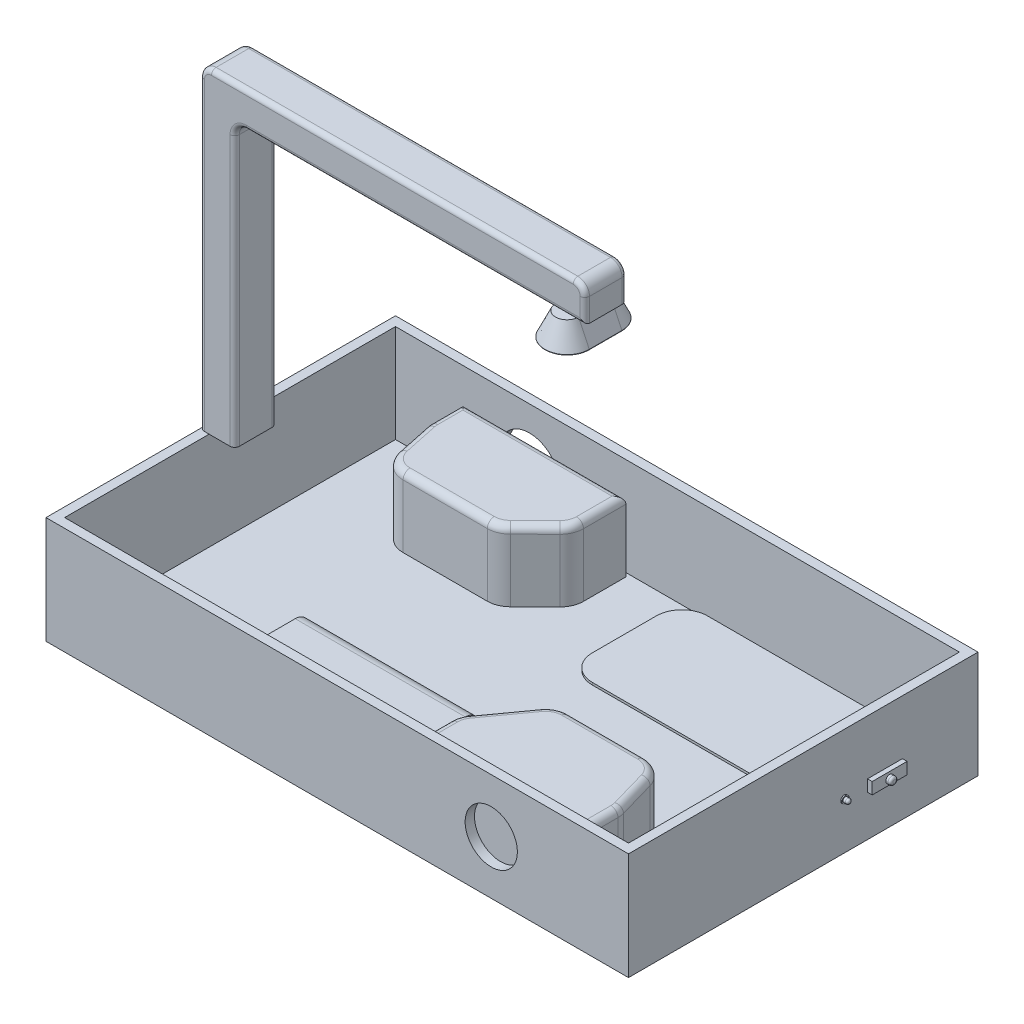
SolidWorks part; units mm, degrees
ref_plane "Front Plane" through (0, 0, 0) normal (0, 0, 1) x (1, 0, 0)
ref_plane "Top Plane" through (0, 0, 0) normal (0, 1, 0) x (1, 0, 0)
ref_plane "Right Plane" through (0, 0, 0) normal (1, 0, 0) x (0, 0, -1)
sketch "Sketch2" plane through (0, 0, 0) normal (0, 1, 0) x (1, 0, 0)
  line L1 (-125, 75) -> (125, 75)
  line L2 (-125, 75) -> (-125, -75)
  line L3 (-125, -75) -> (125, -75)
  line L4 (125, 75) -> (125, -75)
  line L5 (-125, 75) -> (125, -75) construction
  line L6 (-125, -75) -> (125, 75) construction
  point P0 (0, 0)
  dimension "D1" = 150
  dimension "D2" = 250
extrude "Boss-Extrude1" add sketch "Sketch2" along normal blind 4
sketch "Sketch3" plane through (0, 4, 0) normal (0, 1, 0) x (1, 0, 0)
  line L0 (-121, 71) -> (-121, -71)
  line L1 (-125, 75) -> (125, 75)
  line L2 (-125, 75) -> (-125, -75)
  line L3 (-125, -75) -> (125, -75)
  line L4 (125, 75) -> (125, -75)
  line L5 (-121, -71) -> (121, -71)
  line L6 (121, 71) -> (121, -71)
  line L7 (-121, 71) -> (121, 71)
  dimension "D1" = 4
extrude "Boss-Extrude2" add sketch "Sketch3" along normal blind 42
sketch "Sketch4" plane through (0, 0, 0) normal (0, 0, 1) x (1, 0, 0)
  line L0 (-125, 46) -> (-125, 181.8393)
  line L1 (-125, 181.8393) -> (40.2593, 181.8393)
  line L2 (-110, 46) -> (-110, 166.8393)
  line L3 (-110, 166.8393) -> (40.2593, 166.8393)
  line L4 (40.2593, 181.8393) -> (40.2593, 166.8393)
  line L5 (40.2593, 166.8393) -> (40.2593, 165.734)
  line L6 (-110, 46) -> (-125, 46)
  dimension "D1" = 15
extrude "Boss-Extrude3" add sketch "Sketch4" along normal mid plane 18 contours L6 L2 L3 L4 L1 L0
fillet "Fillet1" radius 5 2 edges at (-110, 166.8393, 0) (-125, 181.8393, 0)
fillet "Fillet2" radius 5 1 edges at (40.2593, 181.8393, 0)
fillet "Fillet3" radius 2 16 edges at (-32.3704, 166.8393, -9) (-110, 103.9196, -9) (-110, 103.9196, 9) (-32.3704, 166.8393, 9) (-125, 111.4196, -9) (40.2593, 171.8393, -9) (38.7948, 180.3748, -9) (-42.3704, 181.8393, -9) (40.2593, 171.8393, 9) (38.7948, 180.3748, 9) (-42.3704, 181.8393, 9) (-125, 111.4196, 9) (-108.5355, 165.3748, -9) (-108.5355, 165.3748, 9) (-123.5355, 180.3748, -9) (-123.5355, 180.3748, 9)
sketch "Sketch5" plane through (0, 166.8393, 0) normal (0, -1, 0) x (1, 0, 0)
  line L0 (30.6488, 7) -> (30.6488, -7) construction
  line L1 (-105, -7) -> (40.2593, -7) construction
  line L2 (35.6169, 7) -> (35.6169, -7)
  line L3 (25.6807, 7) -> (25.6807, -7)
  arc A0 (35.6169, 7) -> (25.6807, 7) centre (30.6488, 7) ccw
  arc A1 (25.6807, -7) -> (35.6169, -7) centre (30.6488, -7) ccw
  point P2 (30.6488, 0)
  point P5 (30.6488, 0)
extrude "Boss-Extrude4" add sketch "Sketch5" along normal blind 10 draft 25 draft outward yes
fillet "Fillet4" radius 0.2 4 edges at (40.2799, 156.8393, 0) (30.6488, 156.8393, -16.6312) (21.0176, 156.8393, 0) (30.6488, 156.8393, 16.6312)
sketch "Sketch6" plane through (0, 4, 0) normal (0, 1, 0) x (1, 0, 0)
  line L0 (-90.5005, 69.4211) -> (-20.5005, 69.4211)
  line L1 (-20.5005, 69.4211) -> (-20.5005, 51.1781)
  line L2 (-23.4746, 44.0622) -> (-34.1861, 33.4863)
  line L3 (-41.212, 30.6023) -> (-77.3415, 30.6023)
  line L4 (-87.127, 38.5421) -> (-90.286, 53.5473)
  line L5 (-90.5005, 55.6074) -> (-90.5005, 69.4211)
  arc A0 (-90.286, 53.5473) -> (-90.5005, 55.6074) centre (-80.5005, 55.6074) cw
  arc A1 (-20.5005, 51.1781) -> (-23.4746, 44.0622) centre (-30.5005, 51.1781) cw
  arc A2 (-34.1861, 33.4863) -> (-41.212, 30.6023) centre (-41.212, 40.6023) cw
  arc A3 (-77.3415, 30.6023) -> (-87.127, 38.5421) centre (-77.3415, 40.6023) cw
  dimension "D2" = 10
  dimension "D1" = 70
extrude "Boss-Extrude5" add sketch "Sketch6" along normal blind 30
sketch "Sketch7" plane through (0, 4, 0) normal (0, 1, 0) x (1, 0, 0)
  line L0 (94.2728, -67.9861) -> (24.2728, -67.9861)
  line L1 (94.2728, -67.9861) -> (94.2728, -48.8036)
  line L2 (93.8877, -46.0551) -> (89.3078, -30.034)
  line L3 (79.693, -22.7826) -> (47.1482, -22.7826)
  line L4 (39.0379, -26.9325) -> (26.1625, -44.7826)
  line L5 (24.2728, -50.6326) -> (24.2728, -67.9861)
  arc A0 (94.2728, -48.8036) -> (93.8877, -46.0551) centre (84.2728, -48.8036) ccw
  arc A1 (89.3078, -30.034) -> (79.693, -22.7826) centre (79.693, -32.7826) ccw
  arc A2 (47.1482, -22.7826) -> (39.0379, -26.9325) centre (47.1482, -32.7826) ccw
  arc A3 (26.1625, -44.7826) -> (24.2728, -50.6326) centre (34.2728, -50.6326) ccw
  dimension "D2" = 10
  dimension "D1" = 70
extrude "Boss-Extrude6" add sketch "Sketch7" along normal blind 30
fillet "Fillet5" radius 3 20 edges at (59.2728, 34, 67.9861) (24.2728, 34, 59.3094) (24.7569, 34, 47.5588) (32.6002, 34, 35.8575) (42.593, 34, 23.8803) (63.4206, 34, 22.7826) (85.7144, 34, 24.7987) (91.5978, 34, 38.0446) (94.176, 34, 47.4159) (94.2728, 34, 58.3949) (-55.5005, 34, -69.4211) (-20.5005, 34, -60.2996) (-21.2739, 34, -47.3219) (-28.8303, 34, -38.7742) (-37.4146, 34, -31.3513) (-59.2767, 34, -30.6023) (-83.6422, 34, -32.8369) (-88.7065, 34, -46.0447) (-90.4467, 34, -54.5718) (-90.5005, 34, -62.5142)
sketch "Sketch8" plane through (0, 0, 75) normal (0, 0, 1) x (1, 0, 0)
  circle A0 centre (66.0958, 22.8824) radius 11.2112
extrude "Cut-Extrude1" cut sketch "Sketch8" against normal blind 4
sketch "Sketch9" plane through (0, 0, -75) normal (0, 0, -1) x (-1, 0, 0)
  circle A0 centre (63.5158, 22.2152) radius 12.9775
extrude "Cut-Extrude2" cut sketch "Sketch9" against normal blind 4
sketch "Sketch10" plane through (125, 0, 0) normal (1, 0, 0) x (0, 0, -1)
  line L1 (27.5792, 22.5958) -> (42.5792, 22.5958)
  line L2 (27.5792, 22.5958) -> (27.5792, 17.5958)
  line L3 (27.5792, 17.5958) -> (42.5792, 17.5958)
  line L4 (42.5792, 22.5958) -> (42.5792, 17.5958)
  dimension "D1" = 15
  dimension "D2" = 5
extrude "Boss-Extrude7" add sketch "Sketch10" along normal blind 2
sketch "Sketch11" plane through (127, 0, 0) normal (1, 0, 0) x (0, 0, -1)
  circle A0 centre (35.0792, 19.8125) radius 1.6638
extrude "Boss-Extrude8" add sketch "Sketch11" along normal blind 2
fillet "Fillet6" radius 1 1 edges at (129, 19.8125, -36.743)
sketch "Sketch12" plane through (125, 0, 0) normal (1, 0, 0) x (0, 0, -1)
  circle A0 centre (17.6135, 20.0958) radius 1.523
extrude "Boss-Extrude9" add sketch "Sketch12" along normal blind 0.5
sketch "Sketch13" plane through (125.5, 0, 0) normal (1, 0, 0) x (0, 0, -1)
  circle A0 centre (17.6135, 20.0958) radius 1.0572
extrude "Boss-Extrude10" add sketch "Sketch13" along normal blind 2
fillet "Fillet7" radius 1 1 edges at (127.5, 20.0958, -18.6707)
sketch "Sketch14" plane through (0, 4, 0) normal (0, 1, 0) x (1, 0, 0)
  line L1 (-64.8968, -40.0412) -> (-31.8072, -40.0412)
  line L2 (-64.8968, -40.0412) -> (-64.8968, -53.0407)
  line L3 (-64.8968, -53.0407) -> (-31.8072, -53.0407)
  line L4 (-31.8072, -40.0412) -> (-31.8072, -53.0407)
extrude "Boss-Extrude11" add sketch "Sketch14" along normal blind 3
sketch "Sketch15" plane through (-64.8968, 0, 0) normal (-1, 0, 0) x (0, 0, 1)
  line L0 (64.7681, 9.0213) -> (28.1482, 9.0213) construction
  line L1 (64.7681, 3.0043) -> (28.1482, 3.0043)
  line L2 (64.7681, 15.0382) -> (28.1482, 15.0382)
  arc A0 (64.7681, 3.0043) -> (64.7681, 15.0382) centre (64.7681, 9.0213) ccw
  arc A1 (28.1482, 15.0382) -> (28.1482, 3.0043) centre (28.1482, 9.0213) ccw
  point P2 (46.4582, 8.2272)
  point P3 (46.4582, 9.0213)
extrude "Boss-Extrude12" add sketch "Sketch15" against normal blind 73
sketch "Sketch16" plane through (0, 4, 0) normal (0, 1, 0) x (1, 0, 0)
  line L1 (30.5219, 46.5032) -> (92.9395, 46.5032)
  line L2 (30.5219, 46.5032) -> (30.5219, 22.5282)
  line L3 (30.5219, 22.5282) -> (92.9395, 22.5282)
  line L4 (92.9395, 46.5032) -> (92.9395, 22.5282)
extrude "Boss-Extrude13" add sketch "Sketch16" along normal blind 13 draft 25 draft outward yes
sketch "Sketch17" plane through (0, 17, 0) normal (0, 1, 0) x (1, 0, 0)
  line L1 (14.5117, 58.4118) -> (108.8637, 58.4118)
  line L2 (14.5117, 58.4118) -> (14.5117, 8.9758)
  line L3 (14.5117, 8.9758) -> (108.8637, 8.9758)
  line L4 (108.8637, 58.4118) -> (108.8637, 8.9758)
extrude "Boss-Extrude14" add sketch "Sketch17" along normal blind 1
fillet "Fillet8" radius 11 4 edges at (108.8637, 17.5, -58.4118) (108.8637, 17.5, -8.9758) (14.5117, 17.5, -58.4118) (14.5117, 17.5, -8.9758)
